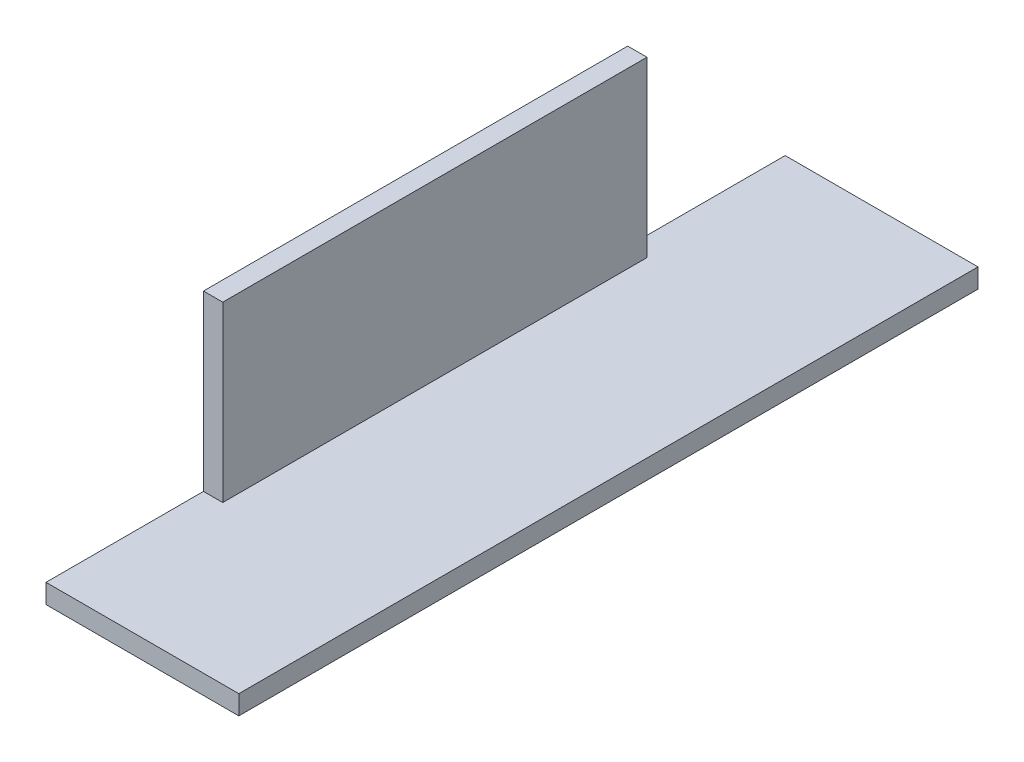
SolidWorks part; units mm, degrees
ref_plane "Спереди" through (0, 0, 0) normal (0, 0, 1) x (1, 0, 0)
ref_plane "Сверху" through (0, 0, 0) normal (0, 1, 0) x (1, 0, 0)
ref_plane "Справа" through (0, 0, 0) normal (1, 0, 0) x (0, 0, -1)
sketch "Эскиз1" plane through (0, 0, 0) normal (0, 0, 1) x (1, 0, 0)
  line L0 (0, 30) -> (0, 0)
  line L1 (0, 0) -> (30, 0)
  line L2 (0, 30) -> (3, 30)
  line L3 (3, 30) -> (3, 3)
  line L4 (3, 3) -> (30, 3)
  line L5 (30, 3) -> (30, 0)
extrude "Бобышка-Вытянуть1" add sketch "Эскиз1" along normal blind 115
sketch "Эскиз2" plane through (0, 0, 0) normal (-1, 0, 0) x (0, 0, 1)
  line L0 (57.5, 32.6572) -> (57.5, -1.9129) construction
  line L1 (0, 30) -> (24.5, 30)
  line L2 (0, 30) -> (0, 3)
  line L3 (0, 3) -> (24.5, 3)
  line L4 (24.5, 30) -> (24.5, 3)
  line L9 (90.5, 30) -> (90.5, 3)
  line L10 (115, 3) -> (90.5, 3)
  line L11 (115, 30) -> (115, 3)
  line L12 (115, 30) -> (90.5, 30)
  point P8 (57.5, 30)
extrude "Вырез-Вытянуть1" cut sketch "Эскиз2" against normal through all
